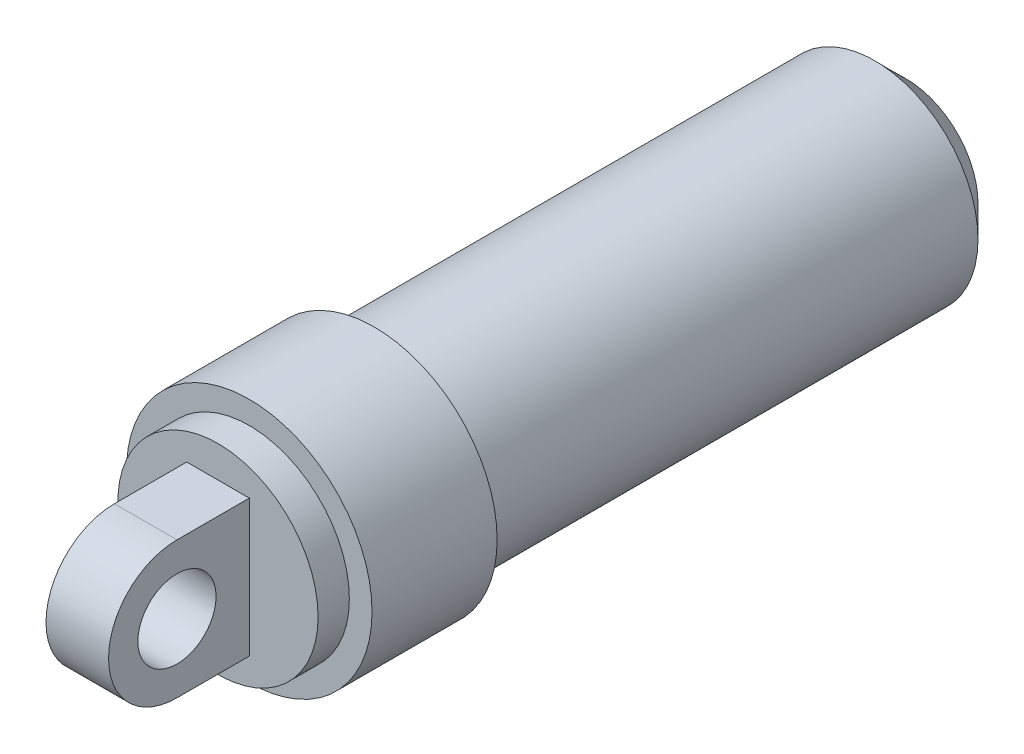
SolidWorks part; units mm, degrees
ref_plane "Front Plane" through (0, 0, 0) normal (0, 0, 1) x (1, 0, 0)
ref_plane "Top Plane" through (0, 0, 0) normal (0, 1, 0) x (1, 0, 0)
ref_plane "Right Plane" through (0, 0, 0) normal (1, 0, 0) x (0, 0, -1)
sketch "Sketch2" plane through (0, 0, 0) normal (0, 0, 1) x (1, 0, 0)
  circle A0 centre (0, 0) radius 6.6
  dimension "D1" = 13.2
extrude "External Shock" add sketch "Sketch2" along normal blind 34
chamfer "Shock Chamfer" distance 2 angle 45 1 edges at (6.6, 0, 0)
sketch "Sketch3" plane through (0, 0, 34) normal (0, 0, 1) x (1, 0, 0)
  circle A0 centre (0, 0) radius 7.85
  dimension "D1" = 15.7
extrude "Cylinder A" add sketch "Sketch3" along normal blind 8
sketch "Sketch4" plane through (0, 0, 42) normal (0, 0, 1) x (1, 0, 0)
  circle A0 centre (0, 0) radius 6.4
  dimension "D1" = 12.8
extrude "Cylinder B" add sketch "Sketch4" along normal blind 2
sketch "Sketch5" plane through (0, 0, 0) normal (1, 0, 0) x (0, 0, -1)
  line L0 (-48.625, -4.375) -> (-44, -4.375)
  line L1 (-44, 6.4) -> (-44, -6.4) construction
  line L2 (-44, -4.375) -> (-44, 4.375)
  line L3 (-44, 4.375) -> (-48.625, 4.375)
  arc A0 (-48.625, -4.375) -> (-48.625, 4.375) centre (-48.625, 0) cw
  point P10 (-53, 0)
  dimension "D1" = 4.375
  dimension "D2" = 9
extrude "Mounting Boss" add sketch "Sketch5" along normal mid plane 4
sketch "Sketch6" plane through (-2, 0, 0) normal (-1, 0, 0) x (0, 0, 1)
  circle A0 centre (48.625, 0) radius 2.5
  arc A1 (48.625, -4.375) -> (48.625, 4.375) centre (48.625, 0) ccw construction
  dimension "D1" = 5
extrude "Mounting Hole" cut sketch "Sketch6" against normal blind 4
sketch "Sketch7" plane through (0, 0, 0) normal (0, 0, -1) x (-1, 0, 0)
  circle A0 centre (0, 0) radius 1.5
  dimension "D1" = 3
extrude "Inner Hole" cut sketch "Sketch7" against normal blind 35
